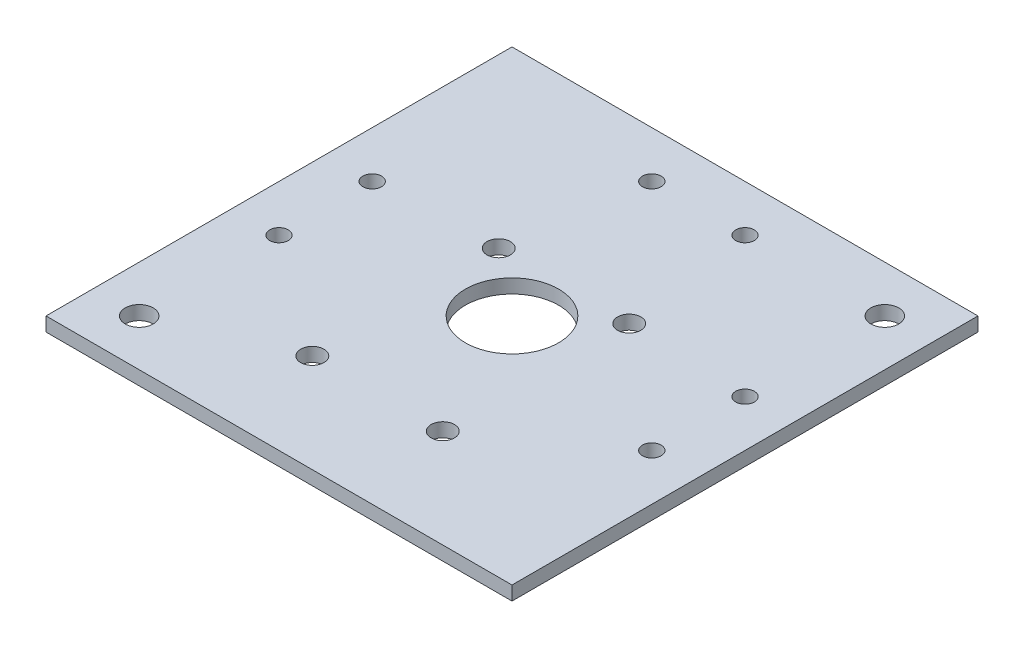
SolidWorks part; units mm, degrees
material "Alloy Steel (SS)"
ref_plane "Front Plane" through (0, 0, 0) normal (0, 0, 1) x (1, 0, 0)
ref_plane "Top Plane" through (0, 0, 0) normal (0, 1, 0) x (1, 0, 0)
ref_plane "Right Plane" through (0, 0, 0) normal (1, 0, 0) x (0, 0, -1)
sketch "Sketch2" plane through (0, 0, 0) normal (0, 1, 0) x (1, 0, 0)
  line L0 (-50, -50) -> (-50, 50)
  line L1 (55, -55) -> (-55, -55)
  line L2 (55, -55) -> (55, 55)
  line L3 (55, 55) -> (-55, 55)
  line L4 (-55, -55) -> (-55, 55)
  line L5 (55, -55) -> (-55, 55) construction
  line L6 (55, 55) -> (-55, -55) construction
  line L7 (50, 50) -> (-50, 50)
  line L8 (50, -50) -> (50, 50)
  line L9 (50, -50) -> (-50, -50)
  point P0 (0, 0)
  dimension "D1" = 110
  dimension "D2" = 110
  dimension "D3" = 5
extrude "Boss-Extrude1" add sketch "Sketch2" along normal blind 89
sketch "Sketch3" plane through (0, 89, 0) normal (0, 1, 0) x (1, 0, 0)
  line L1 (55, -55) -> (-55, -55)
  line L2 (55, -55) -> (55, 55)
  line L3 (55, 55) -> (-55, 55)
  line L4 (-55, -55) -> (-55, 55)
  line L5 (55, -55) -> (-55, 55) construction
  line L6 (55, 55) -> (-55, -55) construction
  point P0 (0, 0)
extrude "Boss-Extrude2" add sketch "Sketch3" along normal blind 8
sketch "Sketch6" plane through (0, 0, 55) normal (0, 0, 1) x (1, 0, 0)
  line L1 (-30, 58) -> (30, 58)
  line L2 (-30, 58) -> (-30, 0)
  line L3 (-30, 0) -> (30, 0)
  line L4 (30, 58) -> (30, 0)
  line L5 (-30, 58) -> (30, 0) construction
  line L6 (-30, 0) -> (30, 58) construction
  point P0 (0, 29)
  point P5 (0, 0)
  dimension "D1" = 58
  dimension "D2" = 60
extrude "Cut-Extrude1" cut sketch "Sketch6" against normal up to next
sketch "Sketch8" plane through (0, 0, 0) normal (0, 0, 1) x (1, 0, 0)
  line L0 (0, 0) -> (0, 97) construction
  line L1 (55, 97) -> (-55, 97) construction
  line L2 (0, 97) -> (-21, 97)
  line L3 (-21, 97) -> (-21, 94.5)
  line L4 (-21, 94.5) -> (-16.2, 94.5)
  line L5 (-16.2, 94.5) -> (-16.2, 88.5)
  line L6 (-16.2, 88.5) -> (0, 88.5)
  line L7 (0, 97) -> (0, 88.5)
  dimension "D1" = 97
  dimension "D2" = 21
  dimension "D3" = 2.5
  dimension "D4" = 4.8
  dimension "D5" = 8.5
  dimension "D6" = 16.2
revolve "Cut-Revolve1" cut sketch "Sketch8" angle 360 about L0
sketch "Sketch9" plane through (0, 58, 0) normal (0, -1, 0) x (1, 0, 0)
  line L1 (55, -55) -> (-55, -55)
  line L2 (55, -55) -> (55, 55)
  line L3 (55, 55) -> (-55, 55)
  line L4 (-55, -55) -> (-55, 55)
  line L5 (55, -55) -> (-55, 55) construction
  line L6 (55, 55) -> (-55, -55) construction
  point P0 (0, 0)
extrude "Boss-Extrude3" add sketch "Sketch9" against normal blind 3
sketch "Sketch10" plane through (0, 61, 0) normal (0, 1, 0) x (1, 0, 0)
  circle A0 centre (0, 0) radius 10
  dimension "D1" = 20
extrude "Cut-Extrude2" cut sketch "Sketch10" against normal up to next
sketch "Sketch11" plane through (0, 0, 0) normal (0, 0, 1) x (1, 0, 0)
  line L0 (-50, 89) -> (-35, 89)
  line L1 (50, 89) -> (-50, 89) construction
  line L2 (-35, 89) -> (-50, 69)
  line L3 (-50, 89) -> (-50, 61) construction
  line L4 (-50, 69) -> (-50, 89)
  dimension "D1" = 15
  dimension "D2" = 20
extrude "Boss-Extrude4" add sketch "Sketch11" along normal mid plane 3
mirror "Mirror1" about plane through (0, 0, 0) normal (1, 0, 0) of "Boss-Extrude4"
sketch "Sketch12" plane through (0, 0, 0) normal (1, 0, 0) x (0, 0, -1)
  line L0 (-35, 89) -> (-50, 89)
  line L1 (-1.5, 89) -> (-50, 89) construction
  line L2 (-50, 89) -> (-50, 69)
  line L3 (-50, 89) -> (-50, 61) construction
  line L4 (-50, 69) -> (-35, 89)
  dimension "D1" = 15
  dimension "20" = 20
extrude "Boss-Extrude5" add sketch "Sketch12" along normal mid plane 3
mirror "Mirror2" about plane through (0, 0, 0) normal (0, 0, 1) of "Boss-Extrude5"
sketch "Sketch14" plane through (0, 97, 0) normal (0, 1, 0) x (1, 0, 0)
  line L0 (55, 55) -> (-55, 55) construction
  line L1 (55, -55) -> (55, 55) construction
  line L2 (-55, 55) -> (-55, -55) construction
  line L3 (-55, -55) -> (55, -55) construction
  circle A0 centre (40, 40) radius 3
  circle A1 centre (-40, -40) radius 3
  dimension "D1" = 6
  dimension "D2" = 15
  dimension "D3" = 15
  dimension "D4" = 15
  dimension "D5" = 15
extrude "Cut-Extrude3" cut sketch "Sketch14" against normal blind 73
sketch "Sketch15" plane through (-50, 0, 0) normal (1, 0, 0) x (0, 0, -1)
  line L0 (-50, 61) -> (50, 61) construction
  line L1 (-50, 61) -> (50, 61) construction
  line L2 (0, 61) -> (0, 66.6519) construction
  line L3 (-25, 63) -> (-23, 63)
  line L4 (-25, 63) -> (-25, 61)
  line L5 (-25, 61) -> (-23, 61)
  line L6 (-23, 63) -> (-23, 61)
  line L7 (25, 61) -> (23, 61)
  line L8 (23, 63) -> (23, 61)
  line L9 (25, 63) -> (23, 63)
  line L10 (25, 63) -> (25, 61)
  point P12 (-24, 61)
  dimension "D1" = 2
  dimension "D2" = 2
  dimension "D3" = 25
extrude "Cut-Extrude4" cut sketch "Sketch15" along normal blind 113 and the other way blind 13
sketch "Sketch16" plane through (0, 61, 0) normal (0, 1, 0) x (1, 0, 0)
  line L0 (0, 0) -> (0, 22.115) construction
  circle A0 centre (-14, 11.15) radius 2.5
  circle A1 centre (-14, -28.85) radius 2.5
  circle A2 centre (14, -28.85) radius 2.5
  circle A3 centre (14, 11.15) radius 2.5
  dimension "D4" = 5
  dimension "D1" = 14
  dimension "D2" = 11.15
  dimension "D3" = 28.85
extrude "Cut-Extrude5" cut sketch "Sketch16" against normal up to next
sketch "Sketch17" plane through (0, 61, 0) normal (0, 1, 0) x (1, 0, 0)
  circle A0 centre (0, 0) radius 11
  circle A1 centre (0, 0) radius 14
  dimension "D1" = 22
  dimension "D2" = 3
extrude "Boss-Extrude6" add sketch "Sketch17" along normal blind 7
sketch "Sketch20" plane through (0, 0, -50) normal (0, 0, 1) x (1, 0, 0)
  line L0 (0, 0) -> (0, 94.5) construction
  line L1 (50, 0) -> (-50, 0) construction
  line L2 (21, 94.5) -> (-21, 94.5) construction
  line L3 (-50, 58) -> (50, 58) construction
  circle A0 centre (10, 48) radius 2
  circle A1 centre (-10, 48) radius 2
  dimension "D1" = 4
  dimension "D2" = 10
  dimension "D3" = 10
extrude "Cut-Extrude8" cut sketch "Sketch20" against normal up to next
sketch "Sketch18" plane through (0, 0, 0) normal (1, 0, 0) x (0, 0, -1)
  line L0 (0, 61) -> (0, 0) construction
  line L1 (10, 61) -> (-10, 61) construction
  line L2 (50, 58) -> (-50, 58) construction
  circle A0 centre (10, 48) radius 2
  circle A2 centre (-10, 48) radius 2
  dimension "D2" = 10
  dimension "5" = 4
  dimension "D1" = 10
extrude "Cut-Extrude6" cut sketch "Sketch18" against normal mid plane 147
sketch "Sketch19" plane through (0, 61, 0) normal (0, 1, 0) x (1, 0, 0)
  line L0 (0, 0) -> (55, 0) construction
  line L1 (55, -55) -> (55, 55) construction
  line L2 (50, 12) -> (50, 8) construction
  line L3 (0, 0) -> (0, 50) construction
  line L4 (-50, 50) -> (50, 50) construction
  circle A0 centre (40, 10) radius 2
  circle A1 centre (40, -10) radius 2
  circle A2 centre (-40, -10) radius 2
  circle A3 centre (-40, 10) radius 2
  circle A4 centre (10, 40) radius 2
  circle A5 centre (-10, 40) radius 2
  dimension "D3" = 4
  dimension "D6" = 4
  dimension "D1" = 10
  dimension "D2" = 10
  dimension "D4" = 10
  dimension "D5" = 10
extrude "Cut-Extrude7" cut sketch "Sketch19" against normal up to next
sketch "Sketch21" plane through (0, 97, 0) normal (0, 1, 0) x (1, 0, 0)
  circle A0 centre (0, 0) radius 21
  circle A1 centre (0, 0) radius 24
  dimension "D1" = 42
  dimension "D2" = 3
extrude "Boss-Extrude7" add sketch "Sketch21" along normal blind 5
sketch "Sketch22" plane through (0, 0, 0) normal (1, 0, 0) x (0, 0, -1)
  line L0 (0, 97) -> (0, 0) construction
  line L1 (-55, 97) -> (55, 97) construction
  dimension "D1" = 97
sketch "Sketch23" plane through (0, 0, 0) normal (0, -1, 0) x (1, 0, 0)
  line L1 (55, -55) -> (-55, -55)
  line L2 (55, -55) -> (55, 55)
  line L3 (55, 55) -> (-55, 55)
  line L4 (-55, -55) -> (-55, 55)
  line L5 (55, -55) -> (-55, 55) construction
  line L6 (55, 55) -> (-55, -55) construction
  point P0 (0, 0)
extrude "Cut-Extrude9" cut sketch "Sketch23" against normal up to surface (58 mm away) up to face at (38, 58, 10)
sketch "Sketch24" plane through (0, 102, 0) normal (0, 1, 0) x (1, 0, 0)
  line L1 (55, -55) -> (-55, -55)
  line L2 (55, -55) -> (55, 55)
  line L3 (55, 55) -> (-55, 55)
  line L4 (-55, -55) -> (-55, 55)
  line L5 (55, -55) -> (-55, 55) construction
  line L6 (55, 55) -> (-55, -55) construction
  point P1 (0, 0)
extrude "Cut-Extrude10" cut sketch "Sketch24" against normal up to surface (34 mm away) up to face at (-14, 68, 0)
sketch "Sketch25" plane through (0, 68, 0) normal (0, 1, 0) x (1, 0, 0)
  line L1 (50, -50) -> (-50, -50)
  line L2 (50, -50) -> (50, 50)
  line L3 (50, 50) -> (-50, 50)
  line L4 (-50, -50) -> (-50, 50)
  line L5 (50, -50) -> (-50, 50) construction
  line L6 (50, 50) -> (-50, -50) construction
  line L7 (55, -55) -> (-55, -55)
  line L8 (55, -55) -> (55, 55)
  line L9 (55, 55) -> (-55, 55)
  line L10 (-55, -55) -> (-55, 55)
  line L11 (55, -55) -> (-55, 55) construction
  line L12 (55, 55) -> (-55, -55) construction
  point P0 (0, 0)
  point P7 (0, 0)
extrude "Cut-Extrude11" cut sketch "Sketch25" against normal up to next
sketch "Sketch26" plane through (0, 68, 0) normal (0, 1, 0) x (1, 0, 0)
  circle A0 centre (0, 0) radius 14
  dimension "D1" = 28
extrude "Cut-Extrude13" cut sketch "Sketch26" against normal up to surface (7 mm away) up to face at (-10, 61, 0)
